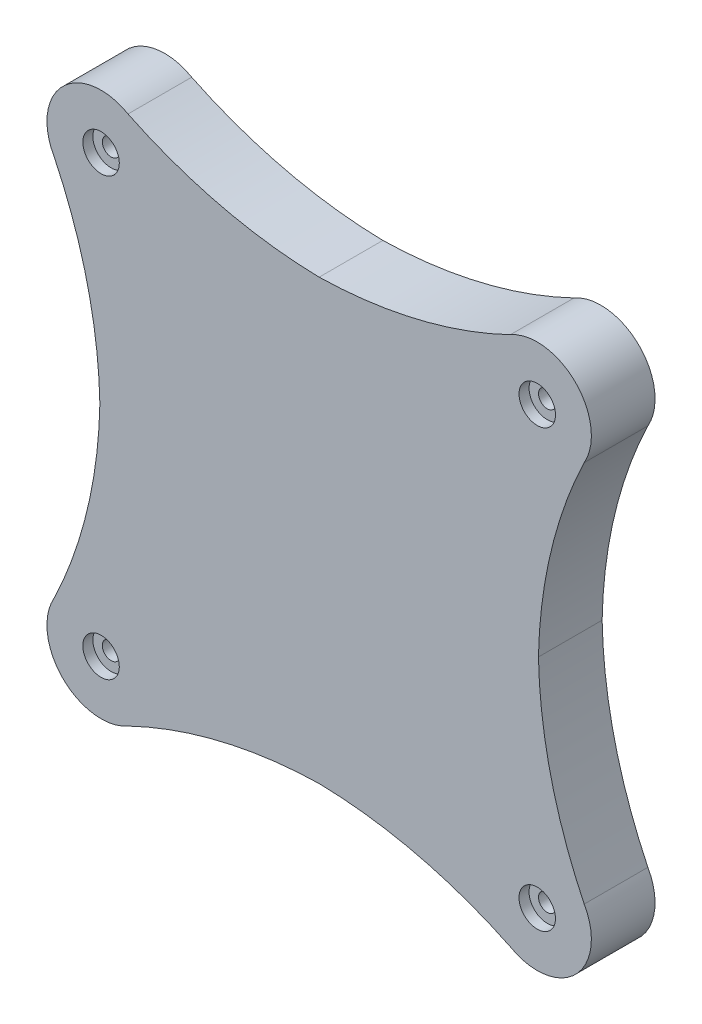
SolidWorks part; units mm, degrees
material "ABS"
ref_plane "Front Plane" through (0, 0, 0) normal (0, 0, 1) x (1, 0, 0)
ref_plane "Top Plane" through (0, 0, 0) normal (0, 1, 0) x (1, 0, 0)
ref_plane "Right Plane" through (0, 0, 0) normal (1, 0, 0) x (0, 0, -1)
sketch "Sketch1" plane through (0, 0, 0) normal (0, 0, 1) x (1, 0, 0)
  circle A5 centre (0, 0) radius 87.4712
extrude "Boss-Extrude1" add sketch "Sketch1" along normal blind 25.4
sketch "Sketch2" plane through (0, 0, 0) normal (0, 0, 1) x (1, 0, 0)
  circle A1 centre (0, 0) radius 69.8436
sketch "Sketch3" plane through (0, 0, 0) normal (0, 0, 1) x (1, 0, 0)
  line L0 (-87.4712, 0) -> (87.4712, 0) construction
  line L1 (0, 0) -> (-61.8515, 61.8515) construction
  line L2 (-61.8515, 61.8515) -> (-102.2627, 102.2627) construction
  line L3 (-86.9962, 86.9962) -> (-78.7341, 106.9428) construction
  line L4 (0, 87.4712) -> (0, -87.4712) construction
  circle A0 centre (0, 0) radius 87.4712 construction
  arc A9 (-76.246, 105.7195) -> (-105.7195, 76.246) centre (-86.9962, 86.9962) ccw
  arc A10 (-76.246, 105.7195) -> (0, 87.4712) centre (3.7574, 271.5829) ccw
  arc A12 (-105.7195, 76.246) -> (-87.4712, 0) centre (-271.5829, -3.7574) cw
  arc A14 (76.246, 105.7195) -> (0, 87.4712) centre (-3.7574, 271.5829) cw
  arc A15 (76.246, 105.7195) -> (105.7195, 76.246) centre (86.9962, 86.9962) cw
  arc A16 (105.7195, 76.246) -> (87.4712, 0) centre (271.5829, -3.7574) ccw
  arc A18 (105.7195, -76.246) -> (87.4712, 0) centre (271.5829, 3.7574) cw
  arc A19 (76.246, -105.7195) -> (105.7195, -76.246) centre (86.9962, -86.9962) ccw
  arc A20 (76.246, -105.7195) -> (0, -87.4712) centre (-3.7574, -271.5829) ccw
  arc A21 (-76.246, -105.7195) -> (0, -87.4712) centre (3.7574, -271.5829) cw
  arc A22 (-76.246, -105.7195) -> (-105.7195, -76.246) centre (-86.9962, -86.9962) cw
  arc A23 (-105.7195, -76.246) -> (-87.4712, 0) centre (-271.5829, 3.7574) ccw
  dimension "D3" = 67.5
  dimension "D4" = 184.15
  dimension "D2" = 43.18
  dimension "D1" = 57.15
extrude "Boss-Extrude2" add sketch "Sketch3" along normal up to surface (25.4 mm away) up to face at (87.4712, 0, 25.4)
sketch "Sketch8" plane through (0, 0, 25.4) normal (0, 0, 1) x (1, 0, 0)
  circle A2 centre (0, 0) radius 72.3836
  circle A3 centre (0, 0) radius 72.3836
  dimension "D1" = 2.54
extrude "Cut-Extrude1" cut sketch "Sketch8" against normal up to next from offset 3.81 offset against normal yes
sketch "Sketch9" plane through (0, 0, 25.4) normal (0, 0, 1) x (1, 0, 0)
  point P0 (86.9962, -86.9962)
  point P1 (-86.9962, -86.9962)
  point P3 (-86.9962, 86.9962)
  point P5 (86.9962, 86.9962)
hole_wizard "CBORE for M6 Hex Head Bolt1" positions "Sketch10" profile "Sketch11" counterbore size "M6" standard "ISO" end condition through all
sketch "Sketch10" plane through (0, 0, 25.4) normal (0, 0, 1) x (1, 0, 0)
  point P0 (-86.9962, 86.9962)
  point P3 (86.9962, 86.9962)
  point P6 (86.9962, -86.9962)
  point P9 (-86.9962, -86.9962)
sketch "Sketch11" plane through (-86.9962, 86.9962, 25.4) normal (1, 0, 0) x (0, -1, 0)
  line L0 (0, 0) -> (0, 25.4)
  line L1 (0, 25.4) -> (3.5, 25.4)
  line L3 (3.5, 25.4) -> (3.5, 4)
  line L4 (3.5, 4) -> (7.2735, 4)
  line L5 (7.2735, 4) -> (7.2735, 0)
  line L7 (7.2735, 0) -> (0, 0)
  line L11 (0, -6.35) -> (0, 107.95) construction
  dimension "Thru Hole Dia." = 7
  dimension "Thru Hole Depth" = 25.4
  dimension "C'Bore Dia." = 14.547
  dimension "C'Bore Depth" = 4
